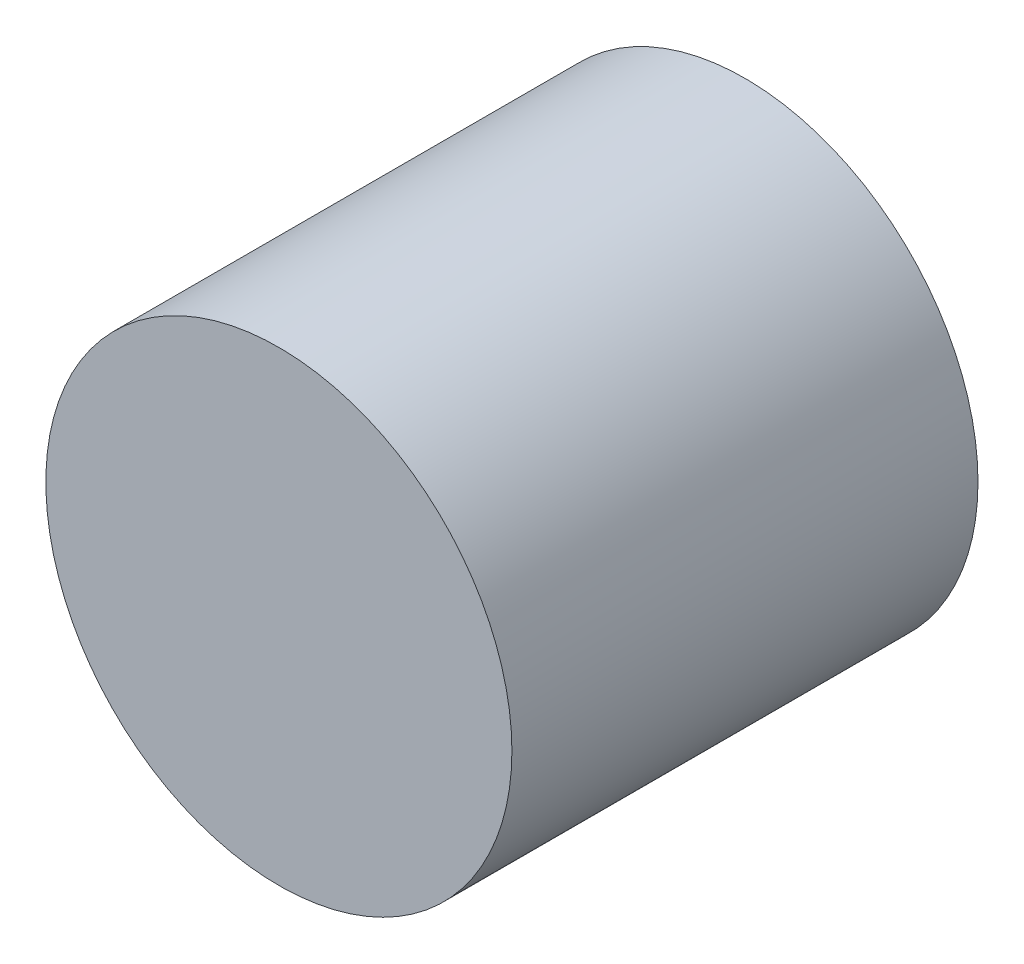
SolidWorks part; units mm, degrees
ref_plane "Front Plane" through (0, 0, 0) normal (0, 0, 1) x (1, 0, 0)
ref_plane "Top Plane" through (0, 0, 0) normal (0, 1, 0) x (1, 0, 0)
ref_plane "Right Plane" through (0, 0, 0) normal (1, 0, 0) x (0, 0, -1)
sketch "Sketch2" plane through (0, 0, 0) normal (0, 0, 1) x (1, 0, 0)
  circle A0 centre (-57.9854, 22.2098) radius 3
extrude "Boss-Extrude1" add sketch "Sketch2" along normal blind 6
